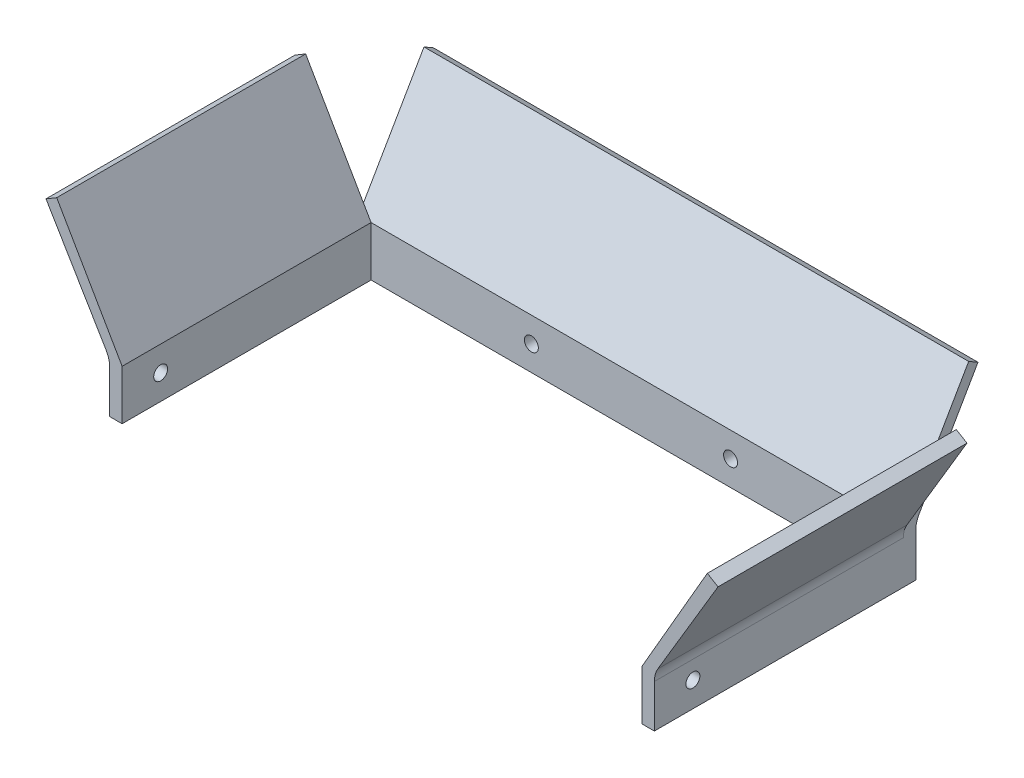
SolidWorks part; units mm, degrees
material "Copper"
ref_plane "Front Plane" through (0, 0, 0) normal (0, 0, 1) x (1, 0, 0)
ref_plane "Top Plane" through (0, 0, 0) normal (0, 1, 0) x (1, 0, 0)
ref_plane "Right Plane" through (0, 0, 0) normal (1, 0, 0) x (0, 0, -1)
sketch "Sketch1" plane through (0, 0, 0) normal (0, 0, 1) x (1, 0, 0)
  line L1 (0, 0) -> (-138.9256, 0)
  line L2 (0, 0) -> (0, -12.7)
  line L3 (0, -12.7) -> (-138.9256, -12.7)
  line L4 (-138.9256, 0) -> (-138.9256, -12.7)
  circle A0 centre (-94.8628, -6.35) radius 1.778
  circle A1 centre (-44.0628, -6.35) radius 1.778
  point P9 (-69.4628, 0)
  dimension "D3" = 3.556
  dimension "D4" = 3.556
  dimension "D5" = 6.35
  dimension "D1" = 138.9256
  dimension "D2" = 12.7
  dimension "D6" = 6.35
  dimension "D7" = 50.8
  dimension "D8" = 25.4
extrude "Boss-Extrude1" add sketch "Sketch1" along normal blind 3.175
sketch "Sketch2" plane through (0, 0, 3.175) normal (0, 0, 1) x (1, 0, 0)
  line L0 (-138.9256, -12.7) -> (0, -12.7) construction
  line L1 (-138.9256, 0) -> (-135.7506, 0)
  line L2 (-138.9256, 0) -> (-138.9256, -12.7)
  line L3 (-138.9256, -12.7) -> (-135.7506, -12.7)
  line L4 (-135.7506, 0) -> (-135.7506, -12.7)
  line L6 (0, 0) -> (-3.175, 0)
  line L7 (0, 0) -> (0, -12.7)
  line L8 (0, -12.7) -> (-3.175, -12.7)
  line L9 (-3.175, 0) -> (-3.175, -12.7)
  dimension "D1" = 3.175
  dimension "D2" = 3.175
extrude "Boss-Extrude2" add sketch "Sketch2" along normal blind 63.5
sketch "Sketch3" plane through (0, 0, 0) normal (1, 0, 0) x (0, 0, -1)
  line L0 (-66.675, 0) -> (0, 0) construction
  line L1 (0, -12.7) -> (0, 0) construction
  circle A0 centre (-56.8402, -6.35) radius 1.778
  dimension "D1" = 3.556
  dimension "D2" = 6.35
  dimension "D3" = 56.8402
extrude "Cut-Extrude1" cut sketch "Sketch3" against normal blind 152.4
sketch "Sketch5" plane through (0, 0, 0) normal (1, 0, 0) x (0, 0, -1)
  line L0 (-3.175, 0) -> (13.4937, 28.8711)
  line L1 (13.4937, 28.8711) -> (15.875, 27.4963)
  line L2 (15.875, 27.4963) -> (0, 0)
  line L5 (-66.675, 0) -> (0, 0) construction
  line L6 (-3.175, 0) -> (0, 0)
  dimension "D1" = 120
  dimension "D2" = 120
  dimension "D3" = 31.75
extrude "Boss-Extrude3" add sketch "Sketch5" against normal up to surface (138.9256 mm away) up to face at (-138.9256, -6.35, 55.0622)
sketch "Sketch6" plane through (0, 0, 66.675) normal (0, 0, 1) x (1, 0, 0)
  line L0 (-3.175, 0) -> (13.5136, 28.9055)
  line L1 (13.5136, 28.9055) -> (16.2417, 27.2813)
  line L2 (16.2417, 27.2813) -> (0, 0)
  line L3 (0, 0) -> (-3.175, 0)
  line L4 (-3.175, 0) -> (-135.7506, 0) construction
  line L5 (-138.9256, 0) -> (-155.1673, 27.2813)
  line L6 (-155.1673, 27.2813) -> (-152.4392, 28.9055)
  line L7 (-152.4392, 28.9055) -> (-135.7506, 0)
  line L8 (-135.7506, 0) -> (-138.9256, 0)
  dimension "D1" = 3.175
  dimension "D2" = 120
  dimension "D3" = 31.75
  dimension "D4" = 3.175
  dimension "D5" = 120
  dimension "D6" = 31.75
extrude "Boss-Extrude4" add sketch "Sketch6" against normal up to surface (63.5 mm away) up to face at (-93.0848, -6.35, 3.175)
fillet "Fillet1" radius 6.35 3 edges at (-138.9256, 0, 34.925) (-69.4628, 0, 0) (0, 0, 34.925)
